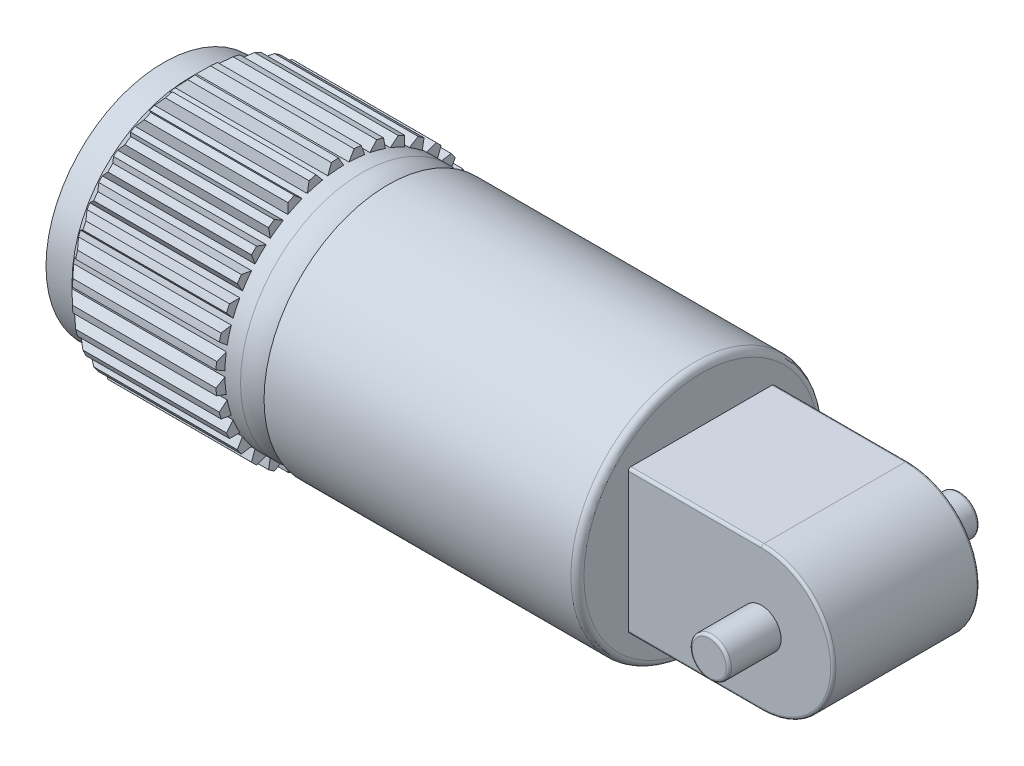
SolidWorks part; units mm, degrees
ref_plane "Спереди" through (0, 0, 0) normal (0, 0, 1) x (1, 0, 0)
ref_plane "Сверху" through (0, 0, 0) normal (0, 1, 0) x (1, 0, 0)
ref_plane "Справа" through (0, 0, 0) normal (1, 0, 0) x (0, 0, -1)
sketch "Эскиз1" plane through (0, 0, 0) normal (0, 0, 1) x (1, 0, 0)
  line L0 (1, 0) -> (20.6, 0)
  line L1 (0, 3.3) -> (0, 4.5)
  line L2 (0, 4.5) -> (1, 4.5)
  line L3 (1, 4.5) -> (1.5, 5)
  line L4 (1.5, 5) -> (7, 5)
  line L5 (7, 5) -> (7, 4.65)
  line L6 (7, 4.65) -> (7.6, 4.65)
  line L7 (8.6, 4.299) -> (8.6, 4.75)
  line L8 (8.6, 4.75) -> (20.6, 4.75)
  line L9 (20.6, 4.75) -> (20.6, 0)
  line L11 (0, 3.3) -> (1, 3.3)
  line L12 (1, 3.3) -> (1, 2.62)
  line L13 (1, 2.62) -> (5, 2.62)
  line L14 (5, 2.62) -> (5, 2.35)
  line L15 (5, 2.35) -> (3, 2.35)
  line L16 (3, 2.35) -> (3, 2.25)
  line L17 (3.05, 0.45) -> (1.45, 0.45)
  line L18 (3, 2.25) -> (3.05, 2.25)
  line L19 (3.05, 2.25) -> (3.05, 0.45)
  arc A0 (7.6, 4.65) -> (8.6, 4.299) centre (7.6, 3.05) cw
  arc A1 (1.45, 0.45) -> (1, 0) centre (1.45, 0) ccw
  dimension "D11" = 1.6
  dimension "D1" = 12
  dimension "D2" = 4.75
  dimension "D3" = 8.6
  dimension "D4" = 4.5
  dimension "D5" = 1
  dimension "D6" = 45
  dimension "D7" = 5
  dimension "D8" = 6
  dimension "D9" = 4.65
  dimension "D10" = 0.6
  dimension "D12" = 3.3
  dimension "D13" = 3
  dimension "D14" = 2.35
  dimension "D15" = 2.62
  dimension "D16" = 1
  dimension "D17" = 5
  dimension "D18" = 0.45
  dimension "D19" = 1
  dimension "D20" = 0.1
  dimension "D21" = 0.05
revolve "Повернуть1" add sketch "Эскиз1" angle 360 about L0
cosmetic thread "Условное изображение резьбы1" parameters "D2"=6
fillet "Скругление1" radius 0.25 1 edges at (20.6, 0, 4.75)
sketch "Эскиз2" plane through (0, 0, 0) normal (0, 0, 1) x (1, 0, 0)
  line L0 (0, 0) -> (20.6, 0) construction
  line L1 (0, 4.5) -> (0, -4.5) construction
  line L2 (20.6, -4.5) -> (20.6, 4.5) construction
  line L4 (20.6, -2.75) -> (25.7, -2.75)
  line L5 (20.6, -2.75) -> (20.6, 2.75)
  line L6 (20.6, 2.75) -> (25.7, 2.75)
  arc A0 (25.7, -2.75) -> (25.7, 2.75) centre (25.7, 0) ccw
  point P13 (28.6, -2.75)
  dimension "D3" = 5.1
  dimension "D1" = 5.5
  dimension "D2" = 8
extrude "Бобышка-Вытянуть1" add sketch "Эскиз2" along normal mid plane 5.6
fillet "Скругление2" radius 0.1 6 edges at (23.15, -2.75, -2.8) (28.45, 0, -2.8) (23.15, -2.75, 2.8) (28.45, 0, 2.8) (23.15, 2.75, -2.8) (23.15, 2.75, 2.8)
sketch "Эскиз3" plane through (0, 0, 2.8) normal (0, 0, 1) x (1, 0, 0)
  line L0 (20.6, 0) -> (25.7, 0) construction
  line L1 (20.6, 2.65) -> (20.6, -2.65) construction
  circle A0 centre (25.7, 0) radius 0.75
  dimension "D1" = 1.5
  dimension "D2" = 5.1
extrude "Бобышка-Вытянуть2" add sketch "Эскиз3" along normal blind 2
fillet "Скругление3" radius 0.1 1 edges at (26.45, 0, 4.8)
mirror "Зеркальное отражение1" about plane through (0, 0, 0) normal (0, 0, 1) of "Скругление3", "Бобышка-Вытянуть2"
sketch "Эскиз4" plane through (7, 0, 0) normal (1, 0, 0) x (0, 0, -1)
  line L0 (0, 0) -> (0, 5) construction
  line L1 (-0.3, 4.991) -> (0, 0) construction
  line L2 (0, 0) -> (0.3, 4.991) construction
  line L3 (-0.3, 4.991) -> (-0.1025, 4.6489)
  line L4 (0.3, 4.991) -> (0.1025, 4.6489)
  circle A0 centre (0, 0) radius 5 construction
  arc A1 (-0.3, 4.991) -> (0.3, 4.991) centre (0, 0) cw
  arc A2 (-0.1025, 4.6489) -> (0.1025, 4.6489) centre (0, 0) cw
  circle A3 centre (0, 0) radius 4.65 construction
  dimension "D1" = 60
  dimension "D2" = 0.6
extrude "Вырез-Вытянуть1" cut sketch "Эскиз4" against normal through all
pattern_circular "Круговой массив1" count 36 over 360 about axis through (0, 0, 0) along (1, 0, 0) of "Вырез-Вытянуть1"
